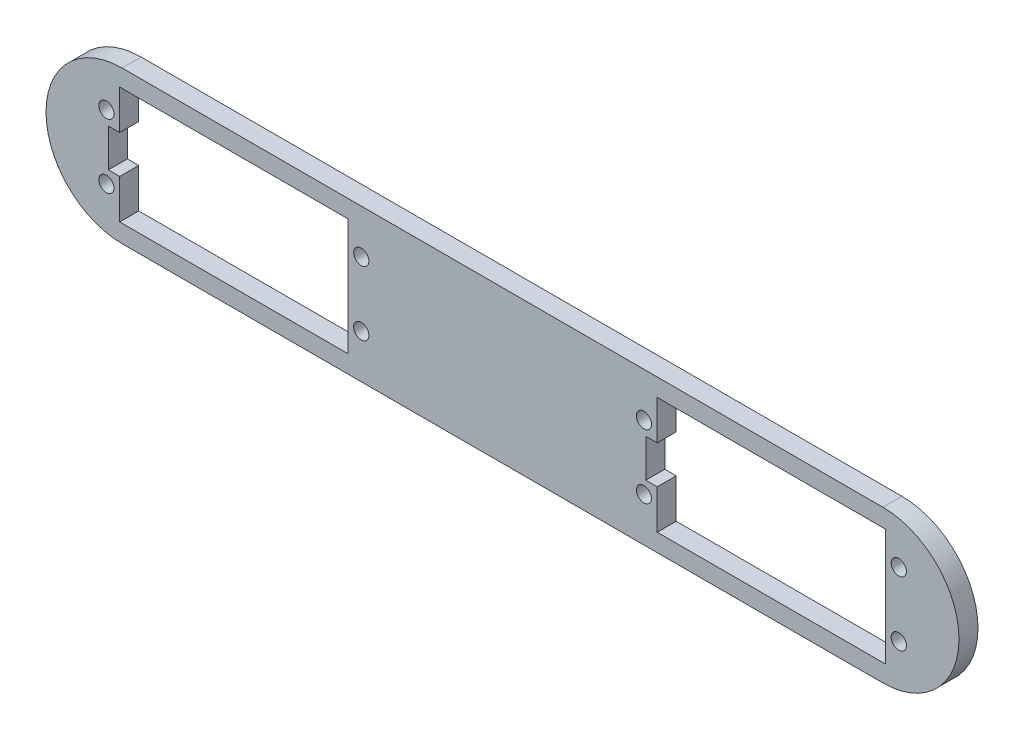
SolidWorks part; units mm, degrees
material "Epoxy, Unfilled"
ref_plane "Front Plane" through (0, 0, 0) normal (0, 0, 1) x (1, 0, 0)
ref_plane "Top Plane" through (0, 0, 0) normal (0, 1, 0) x (1, 0, 0)
ref_plane "Right Plane" through (0, 0, 0) normal (1, 0, 0) x (0, 0, -1)
sketch "Sketch1" plane through (0, 0, 0) normal (0, 0, 1) x (1, 0, 0)
  line L0 (0, 0) -> (200, 0) construction
  line L1 (0, 20) -> (200, 20)
  line L2 (0, -20) -> (200, -20)
  arc A0 (0, 20) -> (0, -20) centre (0, 0) ccw
  arc A1 (200, -20) -> (200, 20) centre (200, 0) ccw
  point P3 (100, 0)
  line B0 (-0.6216, -5) -> (-0.6216, -15.35)
  line B1 (-0.6216, 15.35) -> (59.3784, 15.35)
  line B2 (-0.6216, 15.35) -> (-0.6216, 5)
  line B3 (-0.6216, -15.35) -> (59.3784, -15.35)
  line B4 (59.3784, 15.35) -> (59.3784, -15.35)
  line B5 (-0.6216, 5) -> (-3.6216, 5)
  line B6 (-0.6216, -5) -> (-3.6216, -5)
  line B7 (-3.6216, 5) -> (-3.6216, -5)
  line B8 (140.6727, -5) -> (140.6727, -15.35)
  line B9 (140.6727, 15.35) -> (200.6727, 15.35)
  line B10 (140.6727, 15.35) -> (140.6727, 5)
  line B11 (140.6727, -15.35) -> (200.6727, -15.35)
  line B12 (200.6727, 15.35) -> (200.6727, -15.35)
  line B13 (140.6727, 5) -> (137.6727, 5)
  line B14 (140.6727, -5) -> (137.6727, -5)
  line B15 (137.6727, 5) -> (137.6727, -5)
  dimension "D2" = 20
  dimension "D1" = 200
sketch_block_instance "servo-1"
sketch_block "servo" parameters "D1"=60, "D2"=30.7, "D3"=10, "D4"=3
sketch_block_instance "servo-2"
extrude "Boss-Extrude1" add sketch "Sketch1" along normal blind 5
sketch "Sketch2" plane through (0, 0, 0) normal (0, 0, -1) x (-1, 0, 0)
  circle A0 centre (-137.1727, 8.45) radius 2
  circle A1 centre (-137.1727, -8.45) radius 1.9795
  circle A2 centre (-204.1727, 8.45) radius 2
  circle A3 centre (-204.1727, -8.45) radius 2
extrude "Cut-Extrude1" cut sketch "Sketch2" against normal blind 10
sketch "Sketch3" plane through (0, 0, 0) normal (0, 0, -1) x (-1, 0, 0)
  circle A0 centre (4.1216, 8.45) radius 2
  circle A1 centre (4.1216, -8.45) radius 2
  circle A2 centre (-62.8784, -8.45) radius 2
  circle A3 centre (-62.8784, 8.45) radius 2
extrude "Cut-Extrude2" cut sketch "Sketch3" against normal blind 10
